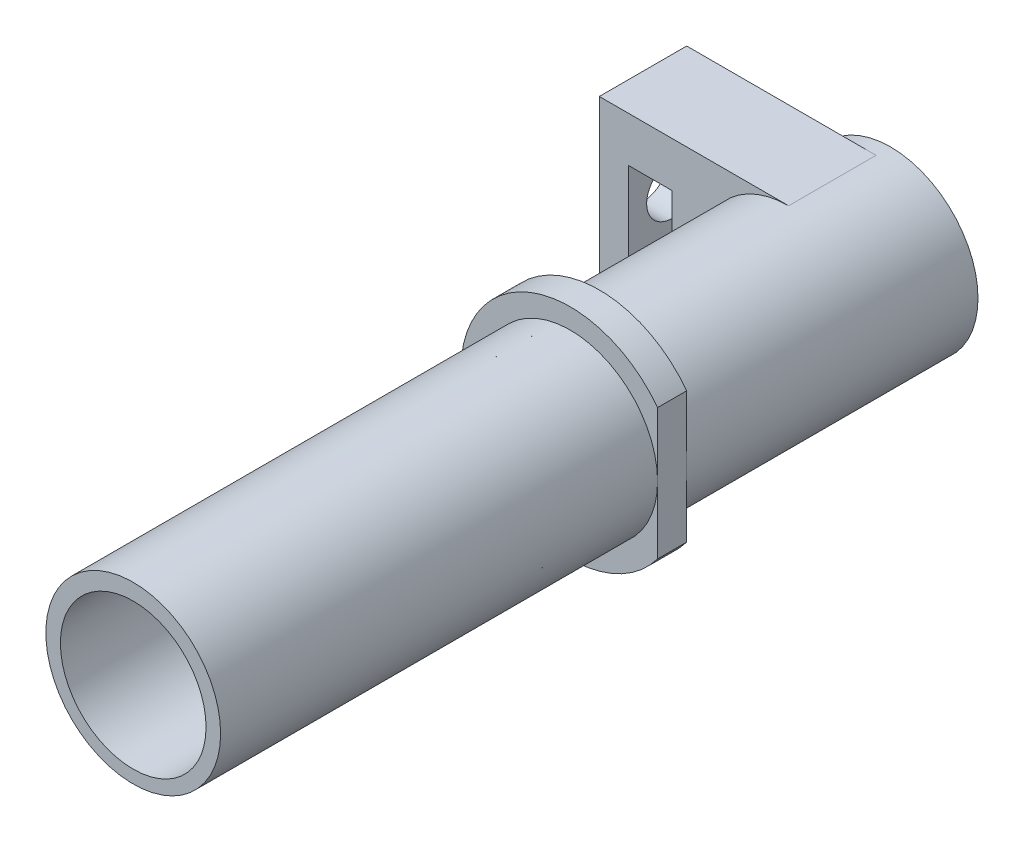
SolidWorks part; units mm, degrees
ref_plane "Plan de face" through (0, 0, 0) normal (0, 0, 1) x (1, 0, 0)
ref_plane "Plan de dessus" through (0, 0, 0) normal (0, 1, 0) x (1, 0, 0)
ref_plane "Plan de droite" through (0, 0, 0) normal (1, 0, 0) x (0, 0, -1)
sketch "Esquisse1" plane through (0, 0, 0) normal (0, 0, 1) x (1, 0, 0)
  circle A0 centre (0, 0) radius 5
  circle A1 centre (0, 0) radius 7.5
extrude "Boss.-Extru.1" add sketch "Esquisse1" along normal blind 2
sketch "Esquisse2" plane through (0, 0, 2) normal (0, 0, 1) x (1, 0, 0)
  circle A0 centre (0, 0) radius 5
  circle A1 centre (0, 0.1143) radius 6
extrude "Boss.-Extru.2" add sketch "Esquisse2" along normal blind 30
sketch "Esquisse3" plane through (0, 0, 0) normal (0, 0, -1) x (-1, 0, 0)
  line L0 (0, 0) -> (-6, 0) construction
  circle A0 centre (0, 0) radius 5
  circle A1 centre (0, 0) radius 6
  point P7 (-6, 0)
extrude "Boss.-Extru.3" add sketch "Esquisse3" along normal blind 20
sketch "Esquisse4" plane through (0, 0, 0) normal (0, 0, -1) x (-1, 0, 0)
  line L0 (-6, 4.5) -> (-6, -4.5)
  arc A0 (-6, 4.5) -> (-6, -4.5) centre (0, 0) ccw
extrude "Enlèv. mat.-Extru.1" cut sketch "Esquisse4" against normal through all
ref_plane "Plan2" through (0, 0, -16) normal (0, 0, -1) x (-1, 0, 0)
sketch "Esquisse6" plane through (0, 0, -16) normal (0, 0, -1) x (-1, 0, 0)
  line L0 (0, -6) -> (0, 6) construction
  line L1 (0, 6) -> (0, 5)
  line L2 (0, -5) -> (0, -6)
  arc A0 (0, 6) -> (0, -6) centre (0, 0) cw
  arc A1 (0, 5) -> (0, -5) centre (0, 0) cw
  circle A2 centre (0, 0) radius 5 construction
  point P7 (0, 0)
extrude "Enlèv. mat.-Extru.2" [suppressed] cut sketch "Esquisse6" against normal mid plane 4
sketch "Esquisse7" plane through (0, 0, -16) normal (0, 0, -1) x (-1, 0, 0)
  line L0 (0, 6) -> (13, 6)
  line L1 (13, 6) -> (13, -6)
  line L2 (13, -6) -> (0, -6)
  arc A0 (0, -6) -> (0, 6) centre (0, 0) ccw
  circle A3 centre (0, 0) radius 6 construction
  point P3 (0, 0)
extrude "Boss.-Extru.4" add sketch "Esquisse7" along normal mid plane 6
sketch "Esquisse8" plane through (-13, 0, 0) normal (-1, 0, 0) x (0, 0, 1)
  line L0 (-13, -6) -> (-19, 6) construction
  circle A0 centre (-16, 0) radius 1.75
extrude "Enlèv. mat.-Extru.3" cut sketch "Esquisse8" against normal blind 16
sketch "Esquisse9" plane through (0, 0, -19) normal (0, 0, -1) x (-1, 0, 0)
  line L0 (9.5, -6) -> (9.5, 6) construction
  line L1 (0, -6) -> (13, -6) construction
  line L2 (13, 6) -> (0, 6) construction
  line L3 (13, -6) -> (13, 6) construction
  line L5 (8, 2.9) -> (11, 2.9)
  line L6 (8, 2.9) -> (8, -2.9)
  line L7 (8, -2.9) -> (11, -2.9)
  line L8 (11, 2.9) -> (11, -2.9)
  line L9 (8, 2.9) -> (11, -2.9) construction
  line L10 (8, -2.9) -> (11, 2.9) construction
  point P8 (9.5, 0)
extrude "Enlèv. mat.-Extru.4" cut sketch "Esquisse9" against normal up to surface (6 mm away) up to face at (-8, 0, -13)
